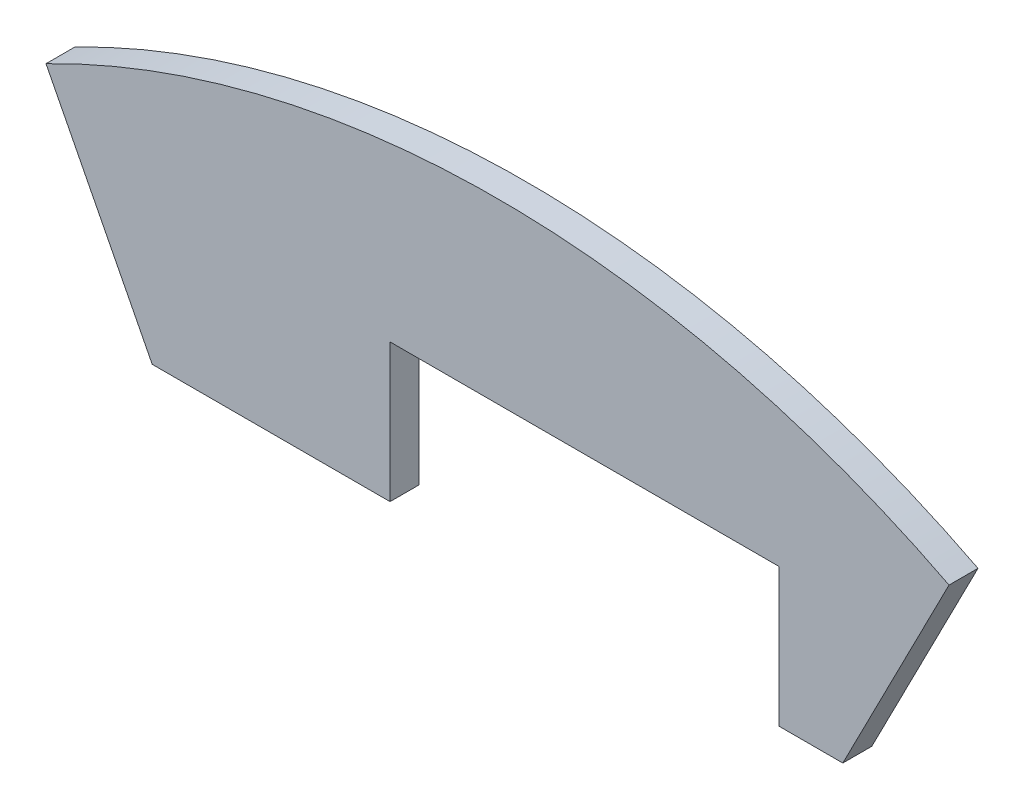
SolidWorks part; units mm, degrees
ref_plane "Front Plane" through (0, 0, 0) normal (0, 0, 1) x (1, 0, 0)
ref_plane "Top Plane" through (0, 0, 0) normal (0, 1, 0) x (1, 0, 0)
ref_plane "Right Plane" through (0, 0, 0) normal (1, 0, 0) x (0, 0, -1)
sketch "Sketch1" plane through (0, 0, 0) normal (0, 0, 1) x (1, 0, 0)
  line L0 (-49.4933, 96.5799) -> (-37.85, 73.8596)
  line L1 (-11.78, 89.0245) -> (30.85, 89.0245)
  line L2 (37.85, 73.8596) -> (49.4933, 96.5799)
  line L3 (0, 0) -> (0, 132.1946) construction
  line L4 (0, -55) -> (0, 55) construction
  line L5 (-37.85, 73.8596) -> (-11.78, 73.8596)
  line L6 (-11.78, 73.8596) -> (-11.78, 89.0245)
  line L8 (30.85, 89.0245) -> (30.85, 73.8596)
  line L9 (30.85, 73.8596) -> (37.85, 73.8596)
  arc A1 (49.4933, 96.5799) -> (-49.4933, 96.5799) centre (0, 0) ccw
  dimension "D1" = 25.53
  dimension "D3" = 42.63
  dimension "D2" = 75.7
  dimension "D4" = 7
extrude "Boss-Extrude1" add sketch "Sketch1" along normal blind 3.175
